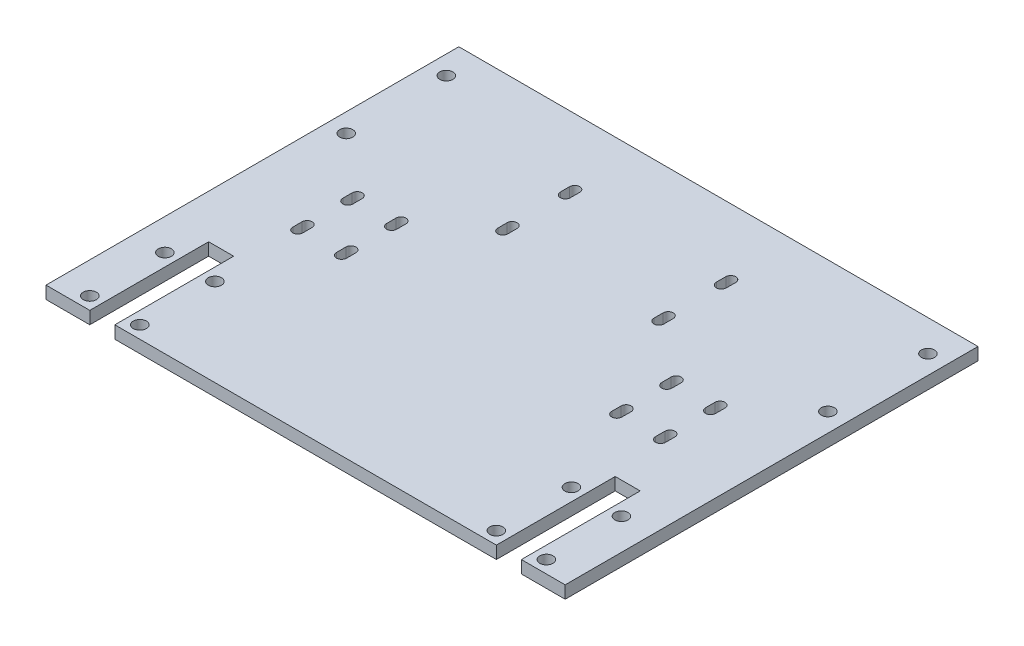
SolidWorks part; units mm, degrees
material "PMMA"
ref_plane "Front Plane" through (0, 0, 0) normal (0, 0, 1) x (1, 0, 0)
ref_plane "Top Plane" through (0, 0, 0) normal (0, 1, 0) x (1, 0, 0)
ref_plane "Right Plane" through (0, 0, 0) normal (1, 0, 0) x (0, 0, -1)
sketch "Sketch1" plane through (0, 0, 0) normal (0, 1, 0) x (1, 0, 0)
  line L0 (0, 42) -> (0, 0) construction
  line L1 (-83, -80) -> (83, -80)
  line L2 (-83, -80) -> (-83, 80)
  line L3 (-83, 80) -> (83, 80)
  line L4 (83, -80) -> (83, 80)
  line L5 (-83, -80) -> (83, 80) construction
  line L6 (-83, 80) -> (83, -80) construction
  line L7 (-77, 10) -> (77, 10) construction
  line L8 (-77, 10) -> (-77, 74) construction
  line L9 (-77, 74) -> (77, 74) construction
  line L10 (77, 10) -> (77, 74) construction
  line L11 (-77, 10) -> (77, 74) construction
  line L12 (-77, 74) -> (77, 10) construction
  circle A0 centre (-77, 74) radius 2.1
  circle A1 centre (-77, 10) radius 2.1
  circle A2 centre (77, 74) radius 2.1
  circle A3 centre (77, 10) radius 2.1
  circle A4 centre (-77, 42) radius 2.1
  circle A5 centre (77, 42) radius 2.1
  point P0 (0, 0)
  point P6 (0, 42)
  dimension "D2" = 4.2
  dimension "D1" = 166
  dimension "D3" = 64
  dimension "D4" = 154
  dimension "D5" = 6
  dimension "D6" = 160
extrude "Boss-Extrude1" add sketch "Sketch1" along normal blind 4
sketch "Sketch2" plane through (0, 4, 0) normal (0, 1, 0) x (1, 0, 0)
  line L0 (0, 0) -> (0, -24.8684) construction
  line L5 (-58, -24.5) -> (-58, -21.5) construction
  line L6 (-59.6, -24.5) -> (-59.6, -21.5)
  line L7 (-56.4, -24.5) -> (-56.4, -21.5)
  line L8 (-44, -24.5) -> (-44, -21.5) construction
  line L9 (-45.6, -24.5) -> (-45.6, -21.5)
  line L10 (-42.4, -24.5) -> (-42.4, -21.5)
  line L11 (-44, -8.5) -> (-44, -5.5) construction
  line L12 (-45.6, -8.5) -> (-45.6, -5.5)
  line L13 (-42.4, -8.5) -> (-42.4, -5.5)
  line L14 (-58, -8.5) -> (-58, -5.5) construction
  line L15 (-59.6, -8.5) -> (-59.6, -5.5)
  line L16 (-56.4, -8.5) -> (-56.4, -5.5)
  line L17 (-58, -24.5) -> (-44, -24.5) construction
  line L18 (-58, -24.5) -> (-58, -8.5) construction
  line L19 (-83, 80) -> (-83, -80) construction
  line L20 (83, 80) -> (-83, 80) construction
  line L21 (58, -24.5) -> (58, -8.5) construction
  line L22 (58, -24.5) -> (44, -24.5) construction
  line L23 (58, -8.5) -> (58, -5.5) construction
  line L24 (59.6, -8.5) -> (59.6, -5.5)
  line L25 (56.4, -8.5) -> (56.4, -5.5)
  line L26 (44, -8.5) -> (44, -5.5) construction
  line L27 (45.6, -8.5) -> (45.6, -5.5)
  line L28 (42.4, -8.5) -> (42.4, -5.5)
  line L29 (44, -24.5) -> (44, -21.5) construction
  line L30 (45.6, -24.5) -> (45.6, -21.5)
  line L31 (42.4, -24.5) -> (42.4, -21.5)
  line L32 (58, -24.5) -> (58, -21.5) construction
  line L33 (59.6, -24.5) -> (59.6, -21.5)
  line L34 (56.4, -24.5) -> (56.4, -21.5)
  arc A0 (-59.6, -24.5) -> (-56.4, -24.5) centre (-58, -24.5) ccw
  arc A1 (-56.4, -21.5) -> (-59.6, -21.5) centre (-58, -21.5) ccw
  arc A2 (-45.6, -24.5) -> (-42.4, -24.5) centre (-44, -24.5) ccw
  arc A3 (-42.4, -21.5) -> (-45.6, -21.5) centre (-44, -21.5) ccw
  arc A4 (-45.6, -8.5) -> (-42.4, -8.5) centre (-44, -8.5) ccw
  arc A5 (-42.4, -5.5) -> (-45.6, -5.5) centre (-44, -5.5) ccw
  arc A6 (-59.6, -8.5) -> (-56.4, -8.5) centre (-58, -8.5) ccw
  arc A7 (-56.4, -5.5) -> (-59.6, -5.5) centre (-58, -5.5) ccw
  arc A8 (59.6, -8.5) -> (56.4, -8.5) centre (58, -8.5) cw
  arc A9 (56.4, -5.5) -> (59.6, -5.5) centre (58, -5.5) cw
  arc A10 (45.6, -8.5) -> (42.4, -8.5) centre (44, -8.5) cw
  arc A11 (42.4, -5.5) -> (45.6, -5.5) centre (44, -5.5) cw
  arc A12 (45.6, -24.5) -> (42.4, -24.5) centre (44, -24.5) cw
  arc A13 (42.4, -21.5) -> (45.6, -21.5) centre (44, -21.5) cw
  arc A14 (59.6, -24.5) -> (56.4, -24.5) centre (58, -24.5) cw
  arc A15 (56.4, -21.5) -> (59.6, -21.5) centre (58, -21.5) cw
  point P2 (-58, -23)
  point P14 (-44, -23)
  point P21 (-44, -7)
  point P28 (-58, -7)
  point P43 (58, -7)
  point P50 (44, -7)
  point P56 (44, -23)
  point P62 (58, -23)
  dimension "D5" = 1.6
  dimension "D3" = 14
  dimension "D4" = 16
  dimension "D6" = 3
  dimension "D7" = 25
  dimension "D8" = 87
  dimension "D1" = 2
  dimension "D2" = 2
extrude "Cut-Extrude1" cut sketch "Sketch2" against normal blind 5
sketch "Sketch3" plane through (0, 4, 0) normal (0, 1, 0) x (1, 0, 0)
  line L0 (-73, -76) -> (-57, -76) construction
  line L1 (-73, -76) -> (-73, -52) construction
  line L2 (0, 0) -> (0, -22.546) construction
  line L3 (-83, -80) -> (83, -80) construction
  line L4 (-83, 80) -> (-83, -80) construction
  line L5 (-57, -52) -> (-73, -76) construction
  line L6 (-69, -42) -> (-61, -42)
  line L7 (-69, -42) -> (-69, -86)
  line L8 (-69, -86) -> (-61, -86)
  line L9 (-61, -42) -> (-61, -86)
  line L10 (-69, -42) -> (-61, -86) construction
  line L11 (-69, -86) -> (-61, -42) construction
  line L12 (69, -86) -> (61, -42) construction
  line L13 (69, -42) -> (61, -86) construction
  line L14 (57, -52) -> (73, -76) construction
  line L15 (73, -76) -> (73, -52) construction
  line L16 (73, -76) -> (57, -76) construction
  line L17 (61, -42) -> (61, -86)
  line L18 (69, -86) -> (61, -86)
  line L19 (69, -42) -> (69, -86)
  line L20 (69, -42) -> (61, -42)
  circle A0 centre (-73, -76) radius 2.1
  circle A1 centre (-57, -76) radius 2.1
  circle A2 centre (-57, -52) radius 2.1
  circle A3 centre (-73, -52) radius 2.1
  circle A4 centre (73, -52) radius 2.1
  circle A5 centre (57, -52) radius 2.1
  circle A6 centre (57, -76) radius 2.1
  circle A7 centre (73, -76) radius 2.1
  point P17 (-65, -64)
  point P34 (65, -64)
  dimension "D5" = 4.2
  dimension "D3" = 16
  dimension "D4" = 24
  dimension "D6" = 4
  dimension "D7" = 10
  dimension "D8" = 8
  dimension "D9" = 22
  dimension "D1" = 2
  dimension "D2" = 2
extrude "Cut-Extrude2" cut sketch "Sketch3" against normal blind 10
sketch "Sketch4" plane through (0, 4, 0) normal (0, 1, 0) x (1, 0, 0)
  line L0 (-83, 80) -> (-83, -80) construction
  line L1 (-83, 52) -> (83, 52)
  line L2 (-83, 52) -> (-83, 80)
  line L3 (-83, 80) -> (83, 80)
  line L4 (83, 52) -> (83, 80)
  circle A0 centre (-77, 42) radius 2.1 construction
  dimension "D1" = 10
extrude "Cut-Extrude3" cut sketch "Sketch4" against normal blind 10
sketch "Sketch5" plane through (0, 4, 0) normal (0, 1, 0) x (1, 0, 0)
  line L1 (-24.95, 9.5) -> (24.95, 9.5) construction
  line L2 (-24.95, 9.5) -> (-24.95, 29.5) construction
  line L3 (-24.95, 29.5) -> (24.95, 29.5) construction
  line L4 (24.95, 9.5) -> (24.95, 29.5) construction
  line L5 (-24.95, 9.5) -> (24.95, 29.5) construction
  line L6 (-24.95, 29.5) -> (24.95, 9.5) construction
  line L7 (-24.95, 28) -> (-24.95, 31) construction
  line L8 (-26.55, 28) -> (-26.55, 31)
  line L9 (-23.35, 28) -> (-23.35, 31)
  line L10 (24.95, 28) -> (24.95, 31) construction
  line L11 (23.35, 28) -> (23.35, 31)
  line L12 (26.55, 28) -> (26.55, 31)
  line L13 (24.95, 8) -> (24.95, 11) construction
  line L14 (23.35, 8) -> (23.35, 11)
  line L15 (26.55, 8) -> (26.55, 11)
  line L16 (-24.95, 8) -> (-24.95, 11) construction
  line L17 (-26.55, 8) -> (-26.55, 11)
  line L18 (-23.35, 8) -> (-23.35, 11)
  line L19 (-83, 52) -> (83, 52) construction
  arc A4 (-26.55, 28) -> (-23.35, 28) centre (-24.95, 28) ccw
  arc A5 (-23.35, 31) -> (-26.55, 31) centre (-24.95, 31) ccw
  arc A6 (23.35, 28) -> (26.55, 28) centre (24.95, 28) ccw
  arc A7 (26.55, 31) -> (23.35, 31) centre (24.95, 31) ccw
  arc A8 (23.35, 8) -> (26.55, 8) centre (24.95, 8) ccw
  arc A9 (26.55, 11) -> (23.35, 11) centre (24.95, 11) ccw
  arc A10 (-26.55, 8) -> (-23.35, 8) centre (-24.95, 8) ccw
  arc A11 (-23.35, 11) -> (-26.55, 11) centre (-24.95, 11) ccw
  point P0 (0, 19.5)
  point P8 (-24.95, 29.5)
  point P15 (24.95, 29.5)
  point P22 (24.95, 9.5)
  point P29 (-24.95, 9.5)
  point P36 (0, 0)
  point P37 (-30.1163, 40.7)
  dimension "D2" = 1.6
  dimension "D3" = 3
  dimension "D4" = 21
  dimension "D1" = 20
  dimension "D5" = 49.9
extrude "Cut-Extrude4" cut sketch "Sketch5" against normal through all
